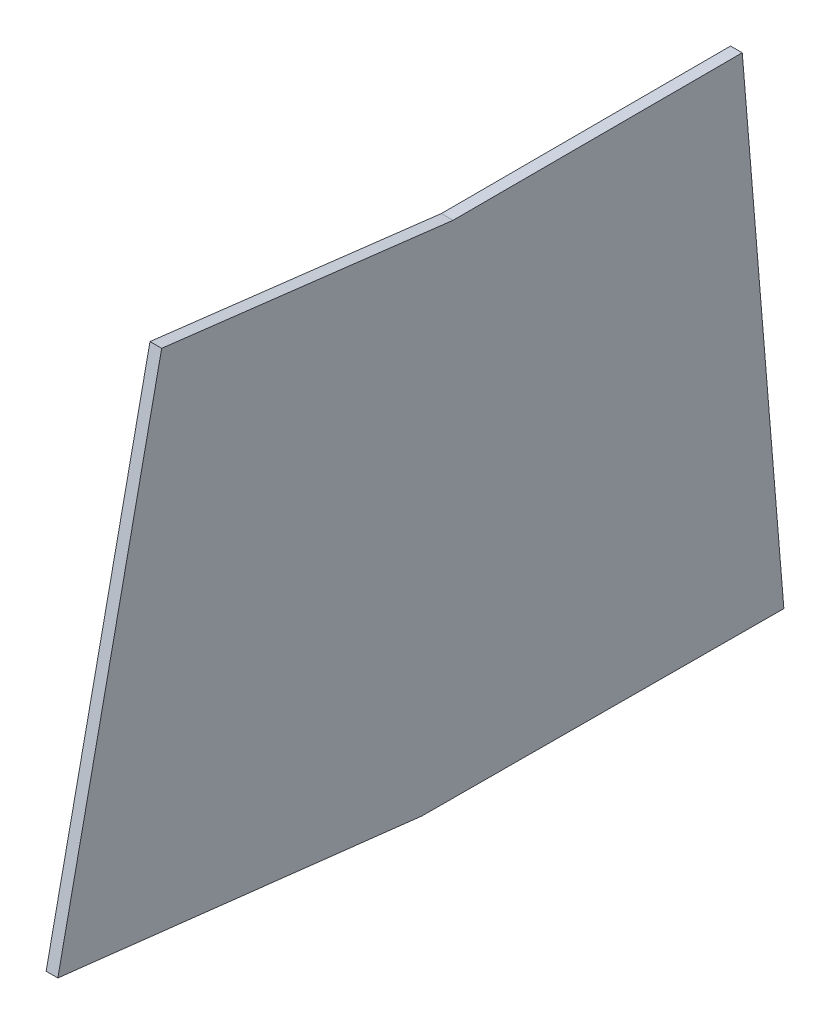
SolidWorks part; units mm, degrees
ref_plane "Front Plane" through (0, 0, 0) normal (0, 0, 1) x (1, 0, 0)
ref_plane "Top Plane" through (0, 0, 0) normal (0, 1, 0) x (1, 0, 0)
ref_plane "Right Plane" through (0, 0, 0) normal (1, 0, 0) x (0, 0, -1)
sketch "Sketch1" plane through (0, 0, 0) normal (1, 0, 0) x (0, 0, -1)
  line L0 (328.8647, -228.5821) -> (19.8155, -227.3824)
  line L1 (19.8155, -227.3824) -> (-291.2817, -191.7359)
  line L2 (-291.2817, -191.7359) -> (-202.5898, 229.7058)
  line L3 (-202.5898, 229.7058) -> (46.3116, 199.9644)
  line L4 (46.3116, 199.9644) -> (293.3175, 200.3851)
  line L5 (293.3175, 200.3851) -> (328.8647, -228.5821)
extrude "Boss-Extrude1" add sketch "Sketch1" along normal blind 10
